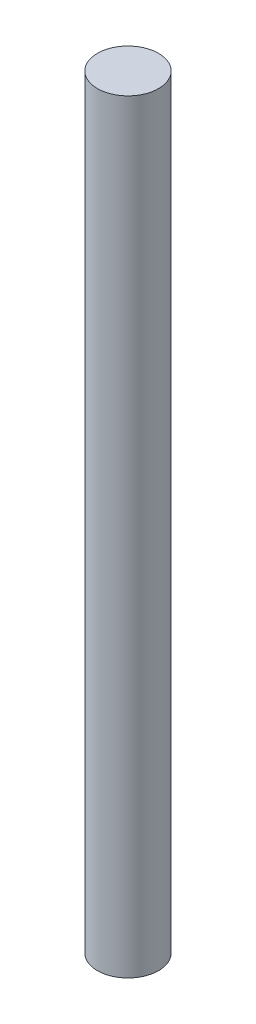
SolidWorks part; units mm, degrees
material "Hexcel AS4C (3000 Filaments)"
ref_plane "Front Plane" through (0, 0, 0) normal (0, 0, 1) x (1, 0, 0)
ref_plane "Top Plane" through (0, 0, 0) normal (0, 1, 0) x (1, 0, 0)
ref_plane "Right Plane" through (0, 0, 0) normal (1, 0, 0) x (0, 0, -1)
sketch "Sketch1" plane through (0, 0, 0) normal (0, 1, 0) x (1, 0, 0)
  circle A0 centre (0, 0) radius 1.6
  dimension "D1" = 3.2
extrude "Boss-Extrude1" add sketch "Sketch1" along normal blind 40 contours A0
